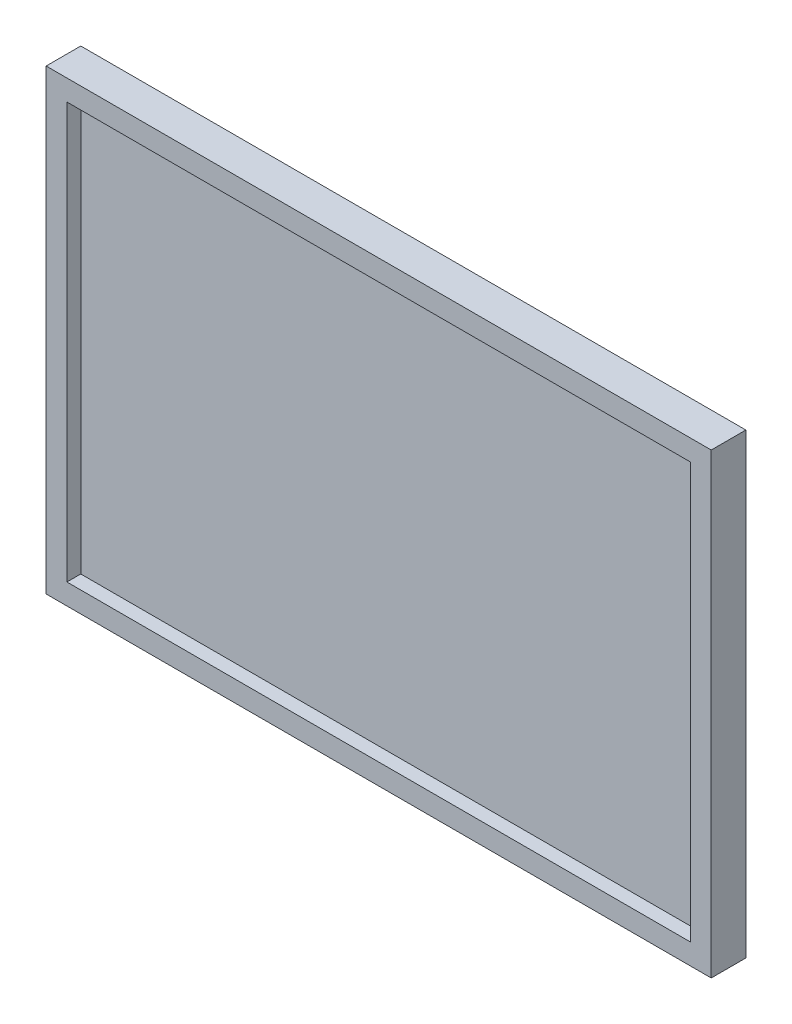
SolidWorks part; units mm, degrees
ref_plane "Front" through (0, 0, 0) normal (0, 0, 1) x (1, 0, 0)
ref_plane "Top" through (0, 0, 0) normal (0, 1, 0) x (1, 0, 0)
ref_plane "Right" through (0, 0, 0) normal (1, 0, 0) x (0, 0, -1)
sketch "Sketch1" plane through (0, 0, 0) normal (0, 0, 1) x (1, 0, 0)
  line L5 (-186, 126) -> (6, 126)
  line L6 (-186, 126) -> (-186, -6)
  line L7 (-186, -6) -> (6, -6)
  line L8 (6, 126) -> (6, -6)
  dimension "D3" = 192
  dimension "D5" = 132
extrude "Boss-Extrude1" add sketch "Sketch1" along normal blind 10 contours L5 L8 L7 L6
sketch "Sketch2" plane through (0, 0, 10) normal (0, 0, 1) x (1, 0, 0)
  line L1 (-180, 120) -> (0, 120)
  line L2 (-180, 120) -> (-180, 0)
  line L3 (-180, 0) -> (0, 0)
  line L4 (0, 120) -> (0, 0)
  dimension "D1" = 180
  dimension "D2" = 120
extrude "Cut-Extrude1" cut sketch "Sketch2" against normal blind 4
